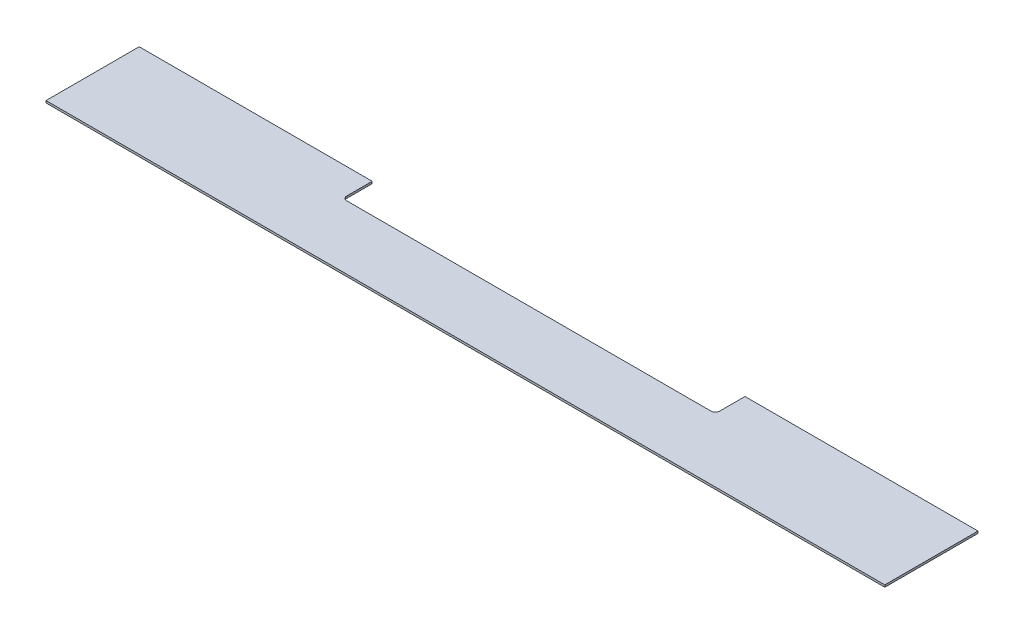
SolidWorks part; units mm, degrees
material "PC High Viscosity"
ref_plane "Front Plane" through (0, 0, 0) normal (0, 0, 1) x (1, 0, 0)
ref_plane "Top Plane" through (0, 0, 0) normal (0, 1, 0) x (1, 0, 0)
ref_plane "Right Plane" through (0, 0, 0) normal (1, 0, 0) x (0, 0, -1)
sketch "Sketch1" plane through (0, 0, 0) normal (0, 1, 0) x (1, 0, 0)
  line L0 (0, 0) -> (1257.3, 0)
  line L1 (0, 0) -> (0, 139.7)
  line L2 (1257.3, 0) -> (1257.3, 139.7)
  line L3 (0, 139.7) -> (1257.3, 139.7)
  dimension "D1" = 1257.3
  dimension "D2" = 139.7
extrude "Boss-Extrude1" add sketch "Sketch1" along normal blind 3.175 contours L0 L2 L3 L1
sketch "Sketch2" plane through (0, 3.175, 0) normal (0, 1, 0) x (1, 0, 0)
  line L0 (349.25, 139.7) -> (908.05, 139.7)
  line L1 (349.25, 139.7) -> (349.25, 95.25)
  line L2 (908.05, 139.7) -> (908.05, 95.25)
  line L3 (349.25, 95.25) -> (908.05, 95.25)
  line L4 (0, 139.7) -> (1257.3, 139.7) construction
  line L5 (0, 0) -> (0, 139.7) construction
  line L6 (1257.3, 0) -> (1257.3, 139.7) construction
  dimension "D1" = 349.25
  dimension "D2" = 349.25
  dimension "D3" = 44.45
extrude "Cut-Extrude1" cut sketch "Sketch2" against normal through all
fillet "Fillet1" radius 6.35 2 edges at (908.05, 1.5875, -95.25) (349.25, 1.5875, -95.25)
